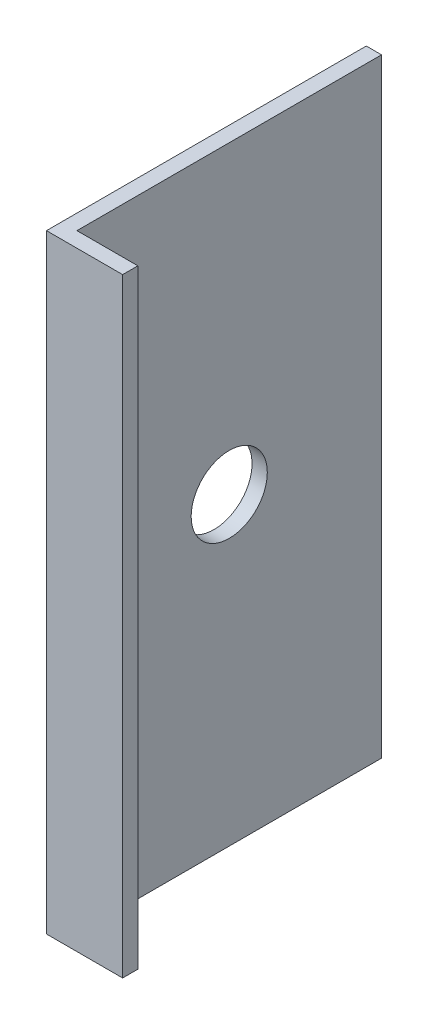
SolidWorks part; units mm, degrees
ref_plane "Спереди" through (0, 0, 0) normal (0, 0, 1) x (1, 0, 0)
ref_plane "Сверху" through (0, 0, 0) normal (0, 1, 0) x (1, 0, 0)
ref_plane "Справа" through (0, 0, 0) normal (1, 0, 0) x (0, 0, -1)
sketch "Эскиз2" plane through (0, 0, 0) normal (0, 1, 0) x (1, 0, 0)
  line L1 (0, 0) -> (10, 0)
  line L2 (0, 0) -> (0, 42)
extrude "Вытянуть-Тонкостенный1" add sketch "Эскиз2" along normal blind 80 thin thin type one direction reverse wall 2
sketch "Эскиз3" plane through (0, 0, 0) normal (-1, 0, 0) x (0, 0, 1)
  circle A0 centre (-22, 40) radius 5
extrude "Вырез-Вытянуть1" cut sketch "Эскиз3" against normal blind 10
